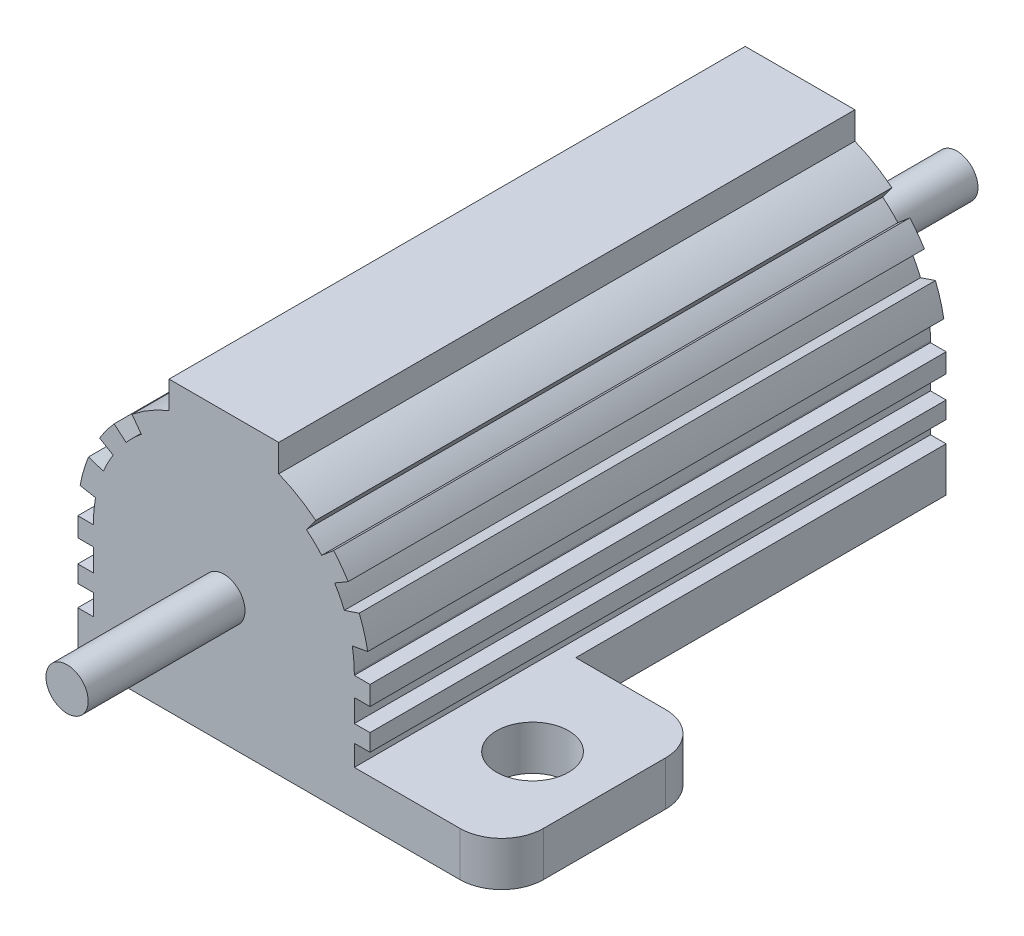
SolidWorks part; units mm, degrees
ref_plane "PLANE-1" through (0, 0, 0) normal (0, 0, 1) x (1, 0, 0)
ref_plane "PLANE-2" through (0, 0, 0) normal (0, 1, 0) x (1, 0, 0)
ref_plane "PLANE-3" through (0, 0, 0) normal (1, 0, 0) x (0, 0, -1)
sketch "Sketch2" plane through (0, 0, 0) normal (0, 0, 1) x (1, 0, 0)
  line L0 (-7.1, 0) -> (7.1, 0)
  line L1 (7.1, 0) -> (7.1, 6.096)
  line L2 (-7.1, 6.096) -> (-7.1, 0)
  line L3 (-2.6654, 14) -> (2.6654, 14)
  line L4 (2.6654, 14) -> (2.6654, 12.6767)
  line L5 (0, 0) -> (0, 12.0544) construction
  line L6 (-2.6654, 14) -> (-2.6654, 12.6767)
  arc A0 (7.1, 6.096) -> (2.6654, 12.6767) centre (0, 6.096) ccw
  arc A1 (-2.6654, 12.6767) -> (-7.1, 6.096) centre (0, 6.096) ccw
  dimension "D1" = 14.2
  dimension "D2" = 6.096
  dimension "D3" = 14
extrude "Extrude1" add sketch "Sketch2" along normal mid plane 28
sketch "Sketch3" plane through (0, 0, 14) normal (0, 0, 1) x (1, 0, 0)
  line L0 (7.1, 4.0043) -> (7.1, 5.1003)
  line L1 (6.237, 7.2231) -> (6.9868, 7.3587)
  line L2 (7.1, 6.0321) -> (7.1, 6.096)
  line L3 (6.338, 2.159) -> (7.1, 2.159)
  line L4 (-7.1, 0) -> (7.1, 0) construction
  line L5 (7.1, 0) -> (7.1, 6.096) construction
  line L6 (6.338, 6.0321) -> (7.1, 6.0321)
  line L7 (6.338, 5.1003) -> (7.1, 5.1003)
  line L8 (6.338, 4.0043) -> (7.1, 4.0043)
  line L9 (6.338, 3.1767) -> (7.1, 3.1767)
  line L10 (6.338, 0) -> (6.338, 6.096)
  line L11 (6.338, 2.159) -> (6.338, 3.1767)
  line L12 (7.1, 2.159) -> (7.1, 3.1767)
  line L14 (4.0126, 11.0021) -> (4.4628, 11.6181)
  line L15 (4.7521, 10.2897) -> (5.333, 10.7831)
  line L16 (5.3819, 9.4434) -> (6.0399, 9.8283)
  line L17 (5.8535, 8.5263) -> (6.5774, 8.7694)
  line L18 (6.338, 4.0043) -> (6.338, 5.1003)
  line L19 (6.338, 6.0321) -> (6.338, 6.096)
  arc A0 (6.5774, 8.7694) -> (6.0399, 9.8283) centre (0, 6.096) ccw
  arc A1 (5.333, 10.7831) -> (4.4628, 11.6181) centre (0, 6.096) ccw
  arc A2 (7.1, 6.096) -> (2.6654, 12.6767) centre (0, 6.096) ccw construction
  arc A3 (6.338, 6.096) -> (2.3794, 11.9704) centre (0, 6.096) ccw
  arc A4 (7.1, 6.096) -> (6.9868, 7.3587) centre (0, 6.096) ccw
  arc A5 (5.8535, 8.5263) -> (5.3819, 9.4434) centre (0, 6.096) ccw
  arc A6 (6.338, 6.096) -> (6.237, 7.2231) centre (0, 6.096) ccw
  arc A7 (4.7521, 10.2897) -> (4.0126, 11.0021) centre (0, 6.096) ccw
  dimension "D2" = 2.159
  dimension "D3" = 0.762
  dimension "D1" = 0.762
sketch "Sketch4" plane through (0, 0, 0) normal (0, -1, 0) x (1, 0, 0)
  line L0 (0, 0) -> (0, -27.3386) construction
  line L1 (-7.1, -4) -> (-13.5, -4)
  line L2 (-7.1, -4) -> (-7.1, -14)
  line L3 (-7.1, -14) -> (-13.5, -14)
  line L4 (-13.5, -4) -> (-13.5, -14)
  line L5 (7.1, 4) -> (13.5, 4)
  line L6 (7.1, 4) -> (7.1, 14)
  line L7 (7.1, 14) -> (13.5, 14)
  line L8 (13.5, 4) -> (13.5, 14)
  dimension "D1" = 27
  dimension "D2" = 10
  dimension "D3" = 10
extrude "Extrude8" add sketch "Sketch4" against normal blind 2.159
fillet "Fillet1" radius 2.032 4 edges at (13.5, 1.0795, 14) (13.5, 1.0795, 4) (-13.5, 1.0795, -14) (-13.5, 1.0795, -4)
extrude "Cut-Extrude1" cut sketch "Sketch3" against normal up to vertex
mirror "Mirror2" about plane through (0, 0, 0) normal (1, 0, 0) of "Cut-Extrude1"
sketch "Sketch5" plane through (0, 2.159, 0) normal (0, 1, 0) x (-1, 0, 0)
  line L3 (0, 0) -> (0, 40.8581) construction
  circle A0 centre (-10, 9) radius 1.75
  circle A1 centre (10, -9) radius 1.75
  dimension "D4" = 3.5
  dimension "D1" = 10
  dimension "D2" = 10
  dimension "D3" = 9
  dimension "D5" = 9
extrude "Cut-Extrude2" cut sketch "Sketch5" against normal through all
sketch "Sketch6" plane through (0, 0, 14) normal (0, 0, 1) x (1, 0, 0)
  circle A0 centre (0, 6.096) radius 1.0262
  dimension "D1" = 2.0523
extrude "Extrude9" add sketch "Sketch6" along normal blind 7.62
mirror "Mirror3" about plane through (0, 0, 0) normal (0, 0, 1) of "Extrude9"
